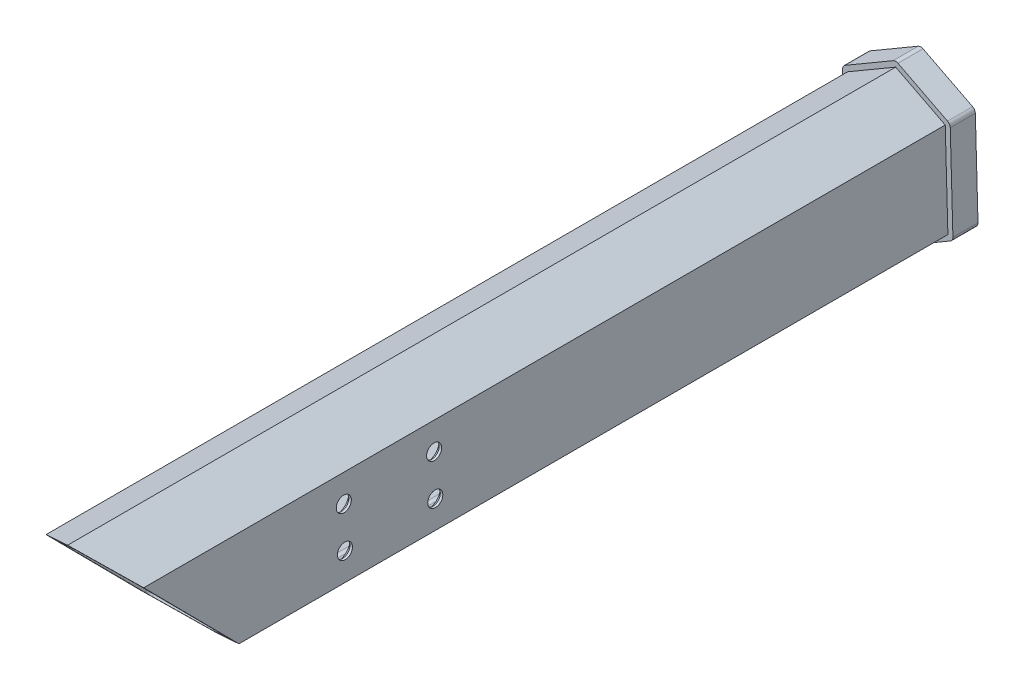
SolidWorks part; units mm, degrees
ref_plane "Front Plane" through (0, 0, 0) normal (0, 0, 1) x (1, 0, 0)
ref_plane "Top Plane" through (0, 0, 0) normal (0, 1, 0) x (1, 0, 0)
ref_plane "Right Plane" through (0, 0, 0) normal (1, 0, 0) x (0, 0, -1)
sketch "Sketch1" plane through (0, 0, 0) normal (0, 0, 1) x (1, 0, 0)
  line L0 (36.798, 101.1427) -> (103.7813, 99.6461) construction
  line L1 (269.9442, 196.2242) -> (270.8412, 164.6209) construction
  line L2 (269.5368, 193.6699) -> (262.4179, 189.5112)
  line L3 (261.9227, 188.6193) -> (262.3999, 171.8048)
  line L4 (262.9449, 170.9425) -> (270.2883, 167.1942)
  line L5 (269.4721, 195.9484) -> (259.893, 190.3524)
  line L6 (259.3978, 189.4606) -> (259.9268, 170.8217)
  line L7 (260.4718, 169.9594) -> (270.3529, 164.9158)
  line L8 (278.3662, 171.3802) -> (271.2473, 167.2215)
  line L9 (280.8911, 170.5389) -> (271.312, 164.943)
  line L10 (278.3842, 189.0866) -> (278.8614, 172.272)
  line L11 (280.8573, 190.0697) -> (281.3863, 171.4307)
  line L12 (270.4958, 193.6971) -> (277.8392, 189.9489)
  line L13 (270.4312, 195.9756) -> (280.3123, 190.932)
  arc A0 (260.4718, 169.9594) -> (259.9268, 170.8217) centre (260.9264, 170.85) cw construction
  arc A1 (259.3978, 189.4606) -> (259.893, 190.3524) centre (260.3974, 189.489) cw construction
  arc A2 (280.8573, 190.0697) -> (280.3123, 190.932) centre (279.8577, 190.0413) ccw construction
  arc A3 (278.8614, 172.272) -> (278.3662, 171.3802) centre (277.8618, 172.2437) cw
  arc A4 (271.2473, 167.2215) -> (270.2883, 167.1942) centre (270.7429, 168.0849) cw
  arc A5 (262.9449, 170.9425) -> (262.3999, 171.8048) centre (263.3995, 171.8332) cw
  arc A6 (278.3842, 189.0866) -> (277.8392, 189.9489) centre (277.3846, 189.0582) ccw
  arc A7 (270.4312, 195.9756) -> (269.4721, 195.9484) centre (269.9765, 195.0849) ccw
  arc A8 (270.4958, 193.6971) -> (269.5368, 193.6699) centre (270.0412, 192.8064) ccw
  arc A9 (280.8911, 170.5389) -> (281.3863, 171.4307) centre (280.3867, 171.4024) ccw
  arc A10 (280.3123, 190.932) -> (280.8573, 190.0697) centre (279.8577, 190.0413) cw
  arc A11 (259.9268, 170.8217) -> (260.4718, 169.9594) centre (260.9264, 170.85) ccw
  arc A12 (261.9227, 188.6193) -> (262.4179, 189.5112) centre (262.9223, 188.6477) cw
  arc A13 (271.312, 164.943) -> (270.3529, 164.9158) centre (270.8076, 165.8064) cw
  arc A14 (259.893, 190.3524) -> (259.3978, 189.4606) centre (260.3974, 189.489) ccw
  point P26 (278.8782, 171.6793)
  point P29 (270.7752, 166.9457)
  point P32 (262.4168, 171.2121)
  point P35 (278.3673, 189.6793)
  point P41 (270.0089, 193.9457)
  point P45 (261.9059, 189.2121)
  point P48 (270.8399, 164.6672)
  dimension "D9" = 1
  dimension "D3" = 1
  dimension "D10" = 1
  dimension "D1" = 67
  dimension "D2" = 23.7
  dimension "D4" = 18
  dimension "D5" = 27
  dimension "D6" = 2.5
  dimension "D7" = 2
  dimension "D8" = 2
extrude "Boss-Extrude1" add sketch "Sketch1" along normal blind 5
sketch "Sketch2" plane through (0, 0, 5) normal (0, 0, 1) x (1, 0, 0)
  line L101 (269.5368, 193.6699) -> (262.4179, 189.5112) construction
  line L102 (277.8392, 189.9489) -> (270.4958, 193.6971) construction
  line L103 (269.5368, 193.6699) -> (262.4179, 189.5112)
  line L104 (277.8392, 189.9489) -> (270.4958, 193.6971)
  line L105 (261.9227, 188.6193) -> (262.3999, 171.8048) construction
  line L106 (261.9227, 188.6193) -> (262.3999, 171.8048)
  line L107 (279.8577, 190.0413) -> (269.9765, 195.0849)
  line L108 (280.3867, 171.4024) -> (279.8577, 190.0413)
  line L109 (270.8076, 165.8064) -> (280.3867, 171.4024)
  line L110 (260.9264, 170.85) -> (270.8076, 165.8064)
  line L111 (260.3974, 189.489) -> (260.9264, 170.85)
  line L112 (269.9765, 195.0849) -> (260.3974, 189.489)
  line L113 (279.8577, 190.0413) -> (269.9765, 195.0849)
  line L114 (280.3867, 171.4024) -> (279.8577, 190.0413)
  line L115 (270.8076, 165.8064) -> (280.3867, 171.4024)
  line L116 (260.9264, 170.85) -> (270.8076, 165.8064)
  line L117 (260.3974, 189.489) -> (260.9264, 170.85)
  line L118 (269.9765, 195.0849) -> (260.3974, 189.489)
  line L119 (278.8614, 172.272) -> (278.3842, 189.0866) construction
  line L120 (271.2473, 167.2215) -> (278.3662, 171.3802) construction
  line L121 (262.9449, 170.9425) -> (270.2883, 167.1942) construction
  line L122 (278.8614, 172.272) -> (278.3842, 189.0866)
  line L123 (271.2473, 167.2215) -> (278.3662, 171.3802)
  line L124 (262.9449, 170.9425) -> (270.2883, 167.1942)
  arc A69 (262.4179, 189.5112) -> (261.9227, 188.6193) centre (262.9223, 188.6477) ccw construction
  arc A70 (270.4958, 193.6971) -> (269.5368, 193.6699) centre (270.0412, 192.8064) ccw construction
  arc A71 (262.4179, 189.5112) -> (261.9227, 188.6193) centre (262.9223, 188.6477) ccw
  arc A72 (270.4958, 193.6971) -> (269.5368, 193.6699) centre (270.0412, 192.8064) ccw
  arc A73 (262.3999, 171.8048) -> (262.9449, 170.9425) centre (263.3995, 171.8332) ccw construction
  arc A74 (262.3999, 171.8048) -> (262.9449, 170.9425) centre (263.3995, 171.8332) ccw
  arc A75 (278.3842, 189.0866) -> (277.8392, 189.9489) centre (277.3846, 189.0582) ccw construction
  arc A76 (278.3662, 171.3802) -> (278.8614, 172.272) centre (277.8618, 172.2437) ccw construction
  arc A77 (270.2883, 167.1942) -> (271.2473, 167.2215) centre (270.7429, 168.0849) ccw construction
  arc A78 (278.3842, 189.0866) -> (277.8392, 189.9489) centre (277.3846, 189.0582) ccw
  arc A79 (278.3662, 171.3802) -> (278.8614, 172.272) centre (277.8618, 172.2437) ccw
  arc A80 (270.2883, 167.1942) -> (271.2473, 167.2215) centre (270.7429, 168.0849) ccw
  dimension "D1" = 1
extrude "Boss-Extrude2" add sketch "Sketch2" along normal blind 165
sketch "Sketch3" plane through (265.5617, 7.5374, 0) normal (-0.9996, -0.0284, 0) x (0, 0, 1)
  line L0 (5, 172.7016) -> (170, 172.7016) construction
  line L1 (5, 182.0248) -> (5, 163.3784) construction
  line L2 (170, 182.0248) -> (170, 163.3784) construction
  line L3 (107, 176.7016) -> (107, 168.7016) construction
  line L4 (125, 176.7016) -> (125, 168.7016) construction
  line L5 (0, 182.0248) -> (0, 163.3784) construction
  line L6 (170, 187.3467) -> (170, 158.0564)
  line L7 (170, 158.0564) -> (141, 158.0564)
  line L8 (170, 158.0564) -> (5, 158.0564) construction
  line L9 (141, 158.0564) -> (170, 187.3467)
  line L10 (5, 163.3784) -> (5, 158.0564) construction
  circle A0 centre (107, 176.7016) radius 1.5
  circle A1 centre (107, 168.7016) radius 1.5
  circle A2 centre (125, 176.7016) radius 1.5
  circle A3 centre (125, 168.7016) radius 1.5
  point P10 (125, 172.7016)
  point P14 (107, 172.7016)
  dimension "D1" = 8
  dimension "D3" = 3
  dimension "D4" = 3
  dimension "D5" = 3
  dimension "D6" = 3
  dimension "D2" = 8
  dimension "D7" = 18
  dimension "D8" = 107
  dimension "D9" = 136
extrude "Cut-Extrude1" cut sketch "Sketch3" against normal blind 165
sketch "Sketch4" plane through (265.5617, 7.5374, 0) normal (-0.9996, -0.0284, 0) x (0, 0, 1)
  line L0 (5, 172.7016) -> (15, 172.7016) construction
  line L1 (5, 182.0248) -> (5, 163.3784) construction
  line L2 (5, 182.0248) -> (5, 163.3784) construction
  circle A0 centre (15, 172.7016) radius 1.5
  dimension "D1" = 3
  dimension "D2" = 10
extrude "Cut-Extrude2" cut sketch "Sketch4" against normal blind 3 contours A0
chamfer "Chamfer1" distance 1 angle 45 9 edges at (278.7788, 175.1815, 107) (278.7788, 175.1815, 125) (278.5519, 183.1783, 107) (278.5519, 183.1783, 125) (262.0053, 185.7099, 125) (262.0053, 185.7099, 107) (262.2322, 177.7131, 107) (262.2322, 177.7131, 125) (262.1187, 181.7115, 15)
ref_plane "Plane3" through (275.2919, 7.8136, 0) normal (0.9996, 0.0284, 0) x (0, 0, -1)
ref_plane "Plane4" through (-4.8998, 172.6321, 0) normal (0.0284, -0.9996, 0) x (-0.9996, -0.0284, 0)
